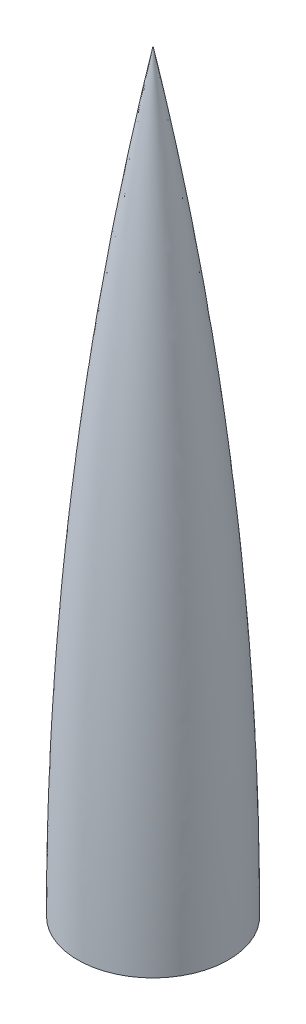
SolidWorks part; units mm, degrees
ref_plane "Front Plane" through (0, 0, 0) normal (0, 0, 1) x (1, 0, 0)
ref_plane "Top Plane" through (0, 0, 0) normal (0, 1, 0) x (1, 0, 0)
ref_plane "Right Plane" through (0, 0, 0) normal (1, 0, 0) x (0, 0, -1)
sketch "Sketch1" plane through (0, 0, 0) normal (1, 0, 0) x (0, 0, -1)
  line L0 (78.359, 0) -> (0, 0)
  line L1 (0, 0) -> (0, 774.2163) construction
  line L2 (78.359, 0) -> (78.359, -50.8) construction
  line L3 (76.2, 0) -> (76.2, -50.8) construction
  line L4 (0, 774.2163) -> (0, 783.59)
  line L5 (0, 732.79) -> (9.906, 732.79)
  line L6 (0, 656.59) -> (23.495, 656.59)
  line L7 (0, 478.79) -> (49.276, 478.79)
  line L8 (0, 326.39) -> (64.8716, 326.39)
  line L9 (0, 173.99) -> (74.5236, 173.99)
  spline S0 degree 3 poles (0, 783.59) (8.5099, 741.3858) (27.2554, 640.1558) (49.3558, 487.6847) (71.7542, 268.9123) (78.3407, 108.9216) (78.359, 0) knots 0 0 0 0 0.163751 0.391528 0.585754 1 1 1 1
  spline S1 degree 3 poles (0, 774.2163) (7.5659, 738.1993) (15.1524, 692.331) (30.4186, 594.332) (45.6116, 481.3488) (71.9335, 269.5684) (75.6791, 108.6466) (76.2, 0) knots 0 0 0 0 0.143276 0.176214 0.383719 0.580852 1 1 1 1
  point P0 (78.359, 0)
  point P3 (0, 783.59)
  point P6 (76.2, 0)
  point P9 (0, 783.59)
  point P21 (70.6717, 326.39)
  point P29 (63.2453, 326.39)
  point P31 (72.8719, 173.99)
  point P33 (0, 0)
  point P35 (0, 775.7116)
  point P37 (4.953, 732.79)
  point P38 (8.0975, 732.79)
  point P39 (0, 0)
  point P40 (20.7142, 656.59)
  point P41 (45.6771, 478.79)
  dimension "D1" = 78.359
  dimension "D2" = 783.59
  dimension "D3" = 127
  dimension "D4" = 50.8
  dimension "D5" = 23.495
  dimension "D6" = 50.8
  dimension "D7" = 9.906
  dimension "D8" = 49.276
  dimension "D9" = 304.8
  dimension "D10" = 76.2
  dimension "D11" = 457.2
  dimension "D12" = 64.8716
  dimension "D13" = 74.5236
  dimension "D14" = 609.6
revolve "Revolve1" add sketch "Sketch1" angle 360 about L1
